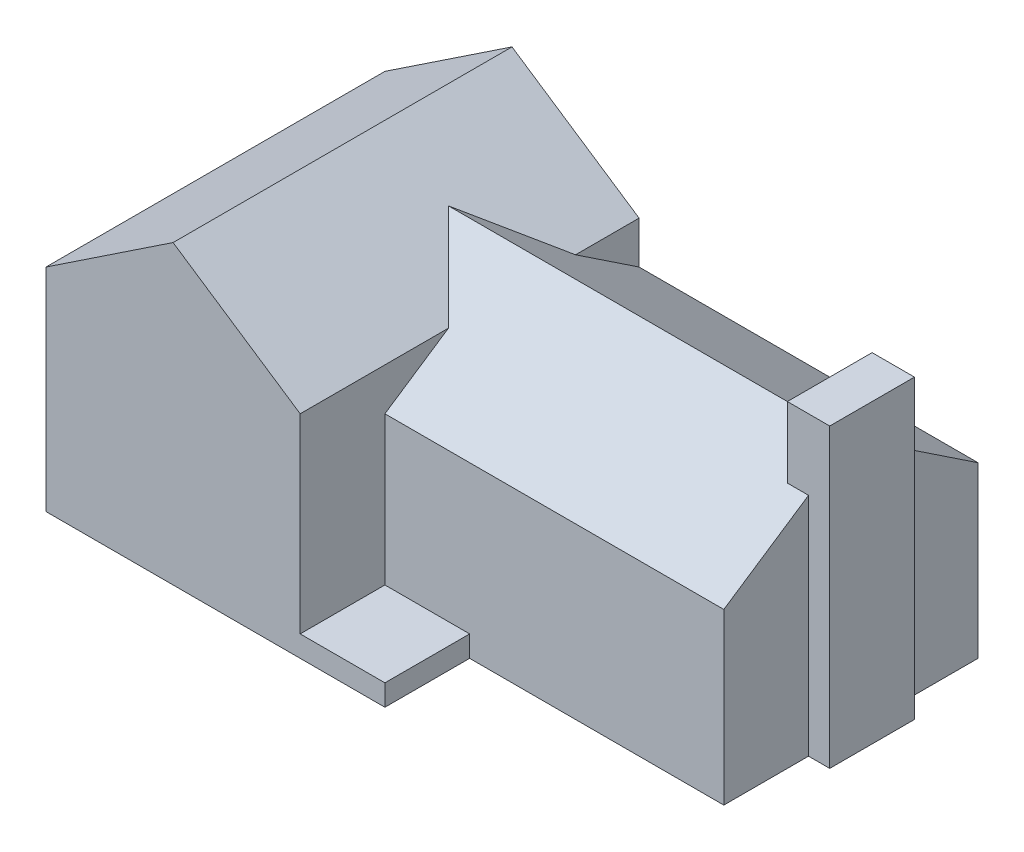
SolidWorks part; units mm, degrees
ref_plane "Front Plane" through (0, 0, 0) normal (0, 0, 1) x (1, 0, 0)
ref_plane "Top Plane" through (0, 0, 0) normal (0, 1, 0) x (1, 0, 0)
ref_plane "Right Plane" through (0, 0, 0) normal (1, 0, 0) x (0, 0, -1)
sketch "Sketch1" plane through (0, 0, 0) normal (0, 1, 0) x (1, 0, 0)
  line L1 (0, 0) -> (30, 0)
  line L2 (0, 0) -> (0, 40)
  line L3 (0, 40) -> (30, 40)
  line L4 (30, 0) -> (30, 40)
  dimension "D1" = 30
  dimension "D2" = 40
extrude "Boss-Extrude1" add sketch "Sketch1" along normal blind 25
sketch "Sketch2" plane through (0, 0, 0) normal (0, 0, 1) x (1, 0, 0)
  line L0 (15, 25) -> (15, 35) construction
  line L1 (0, 25) -> (30, 25) construction
  line L2 (15, 25) -> (30, 25)
  line L3 (30, 25) -> (15, 35)
  line L4 (15, 35) -> (0, 25)
  line L5 (0, 25) -> (15, 25)
  dimension "D1" = 10
extrude "Boss-Extrude2" add sketch "Sketch2" against normal blind 40
sketch "Sketch3" plane through (0, 0, 0) normal (0, -1, 0) x (-1, 0, 0)
  line L1 (-30, 0) -> (-40, 0)
  line L2 (-30, 0) -> (-30, 40)
  line L3 (-30, 40) -> (-40, 40)
  line L4 (-40, 0) -> (-40, 40)
  dimension "D1" = 40
  dimension "D2" = 10
extrude "Boss-Extrude3" add sketch "Sketch3" against normal blind 2.5
sketch "Sketch4" plane through (30, 0, 0) normal (1, 0, 0) x (0, 0, -1)
  line L0 (0, 0) -> (10, 0) construction
  line L1 (40, 0) -> (0, 0) construction
  line L2 (40, 25) -> (40, 20) construction
  line L3 (40, 25) -> (40, 2.5) construction
  line L5 (10, 0) -> (40, 0)
  line L6 (10, 0) -> (10, 20)
  line L7 (10, 20) -> (40, 20)
  line L8 (40, 0) -> (40, 20)
  dimension "D1" = 10
  dimension "D2" = 5
extrude "Boss-Extrude4" add sketch "Sketch4" along normal blind 40
sketch "Sketch5" plane through (70, 0, 0) normal (1, 0, 0) x (0, 0, -1)
  line L0 (25, 20) -> (25, 30) construction
  line L1 (40, 20) -> (10, 20) construction
  line L2 (25, 20) -> (10, 20)
  line L3 (10, 20) -> (25, 30)
  line L4 (25, 30) -> (40, 20)
  line L5 (40, 20) -> (25, 20)
  dimension "D1" = 10
extrude "Boss-Extrude5" add sketch "Sketch5" against normal blind 55
sketch "Sketch6" plane through (70, 0, 0) normal (1, 0, 0) x (0, 0, -1)
  line L0 (10, 0) -> (20, 0) construction
  line L1 (10, 0) -> (40, 0) construction
  line L3 (20, 0) -> (30, 0)
  line L4 (20, 0) -> (20, 35)
  line L5 (20, 35) -> (30, 35)
  line L6 (30, 0) -> (30, 35)
  dimension "D1" = 10
  dimension "D2" = 10
  dimension "D3" = 35
extrude "Boss-Extrude7" add sketch "Sketch6" along normal blind 2.5 and the other way blind 2.5
